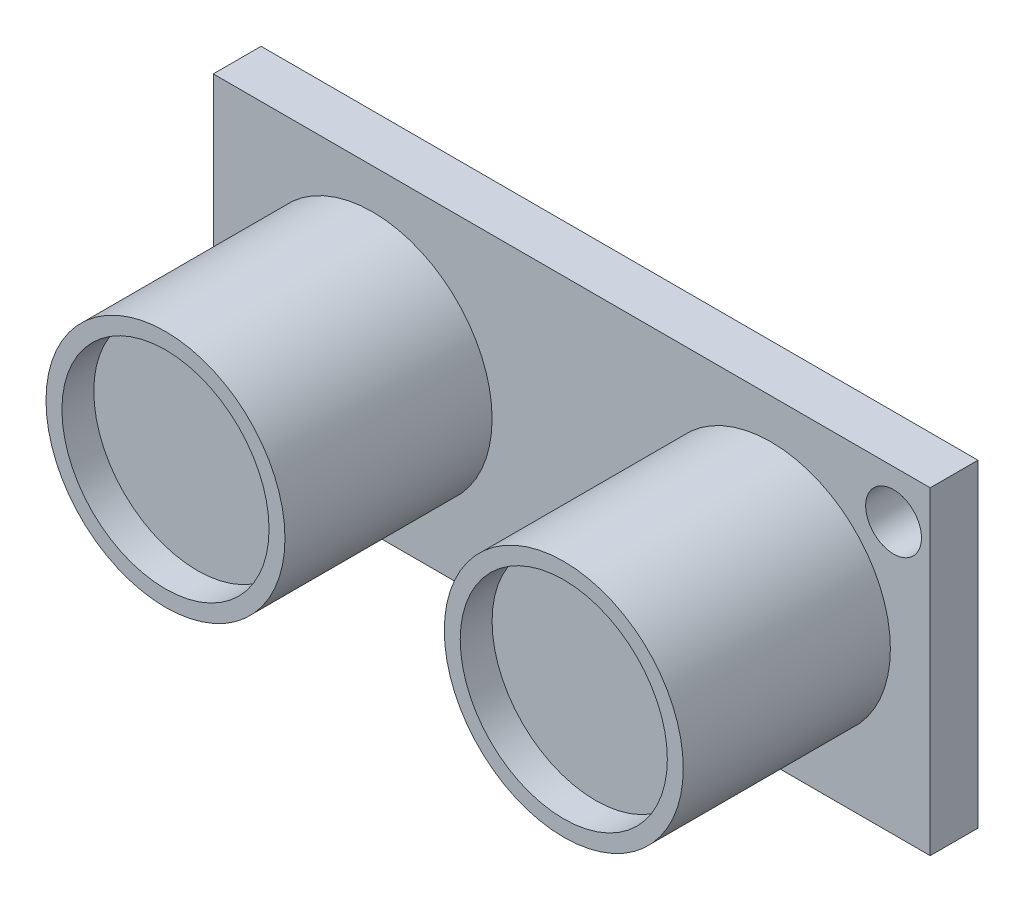
SolidWorks part; units mm, degrees
material "E-玻璃纤维"
ref_plane "前视基准面" through (0, 0, 0) normal (0, 0, 1) x (1, 0, 0)
ref_plane "上视基准面" through (0, 0, 0) normal (0, 1, 0) x (1, 0, 0)
ref_plane "右视基准面" through (0, 0, 0) normal (1, 0, 0) x (0, 0, -1)
sketch "草图1" plane through (0, 0, 0) normal (0, 0, 1) x (1, 0, 0)
  line L1 (-22.5, 10) -> (22.5, 10)
  line L2 (-22.5, 10) -> (-22.5, -10)
  line L3 (-22.5, -10) -> (22.5, -10)
  line L4 (22.5, 10) -> (22.5, -10)
  line L5 (0, -10) -> (0, 10) construction
  line L6 (-22.5, 0) -> (22.5, 0) construction
  point P0 (0, 0)
  dimension "D1" = 45
  dimension "D2" = 20
extrude "凸台-拉伸1" add sketch "草图1" along normal blind 3
sketch "草图2" plane through (0, 0, 3) normal (0, 0, 1) x (1, 0, 0)
  line L0 (0, 10) -> (0, -19.1639) construction
  line L1 (22.5, 10) -> (-22.5, 10) construction
  line L2 (22.5, -10) -> (22.5, 10) construction
  circle A0 centre (12.5, 0) radius 7.5
  circle A1 centre (-12.5, 0) radius 7.5
  dimension "D1" = 15
  dimension "D2" = 10
  dimension "D3" = 10
extrude "凸台-拉伸2" add sketch "草图2" along normal blind 13
sketch "草图3" plane through (0, 0, 3) normal (0, 0, 1) x (1, 0, 0)
  line L0 (0, 14.6163) -> (0, -13.8655) construction
  line L1 (-21.5741, 0) -> (-11.4127, 0) construction
  line L2 (22.5, 10) -> (-22.5, 10) construction
  circle A0 centre (20.2, 7) radius 1.75
  circle A2 centre (-20.2, -7) radius 1.75
  dimension "D1" = 3.5
  dimension "D2" = 3
extrude "切除-拉伸1" cut sketch "草图3" against normal through all both and the other way through all
sketch "草图4" plane through (0, 0, 16) normal (0, 0, 1) x (1, 0, 0)
  circle A0 centre (-12.5, 0) radius 7.5 construction
  circle A1 centre (12.5, 0) radius 7.5 construction
  circle A2 centre (-12.5, 0) radius 7.5
  circle A3 centre (12.5, 0) radius 7.5
  circle A4 centre (-12.5, 0) radius 6.5
  circle A5 centre (12.5, 0) radius 6.5
  dimension "D1" = 1
extrude "切除-拉伸2" cut sketch "草图4" against normal blind 2 contours A4 | A5
